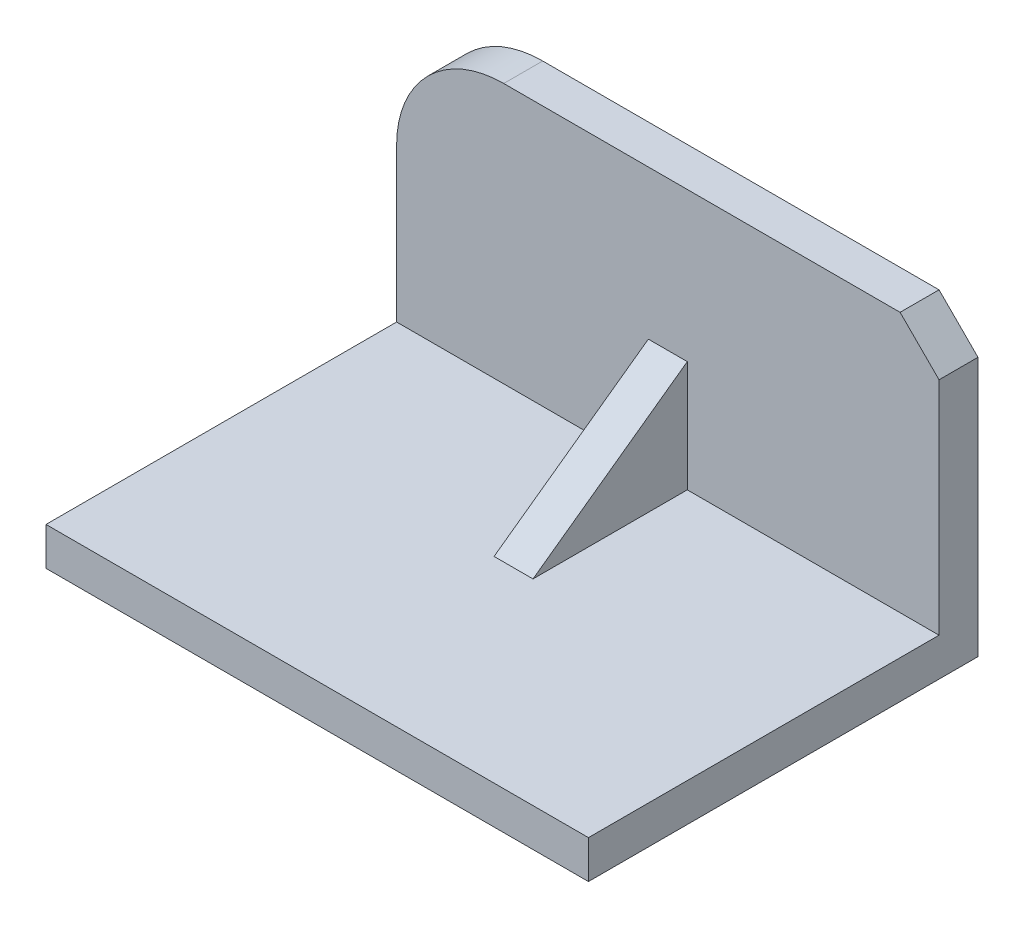
SolidWorks part; units mm, degrees
ref_plane "Front Plane" through (0, 0, 0) normal (0, 0, 1) x (1, 0, 0)
ref_plane "Top Plane" through (0, 0, 0) normal (0, 1, 0) x (1, 0, 0)
ref_plane "Right Plane" through (0, 0, 0) normal (1, 0, 0) x (0, 0, -1)
sketch "Sketch1" plane through (0, 0, 0) normal (0, 0, 1) x (1, 0, 0)
  line L1 (-42.1183, 38.2775) -> (69.6255, 38.2775)
  line L2 (-69.6255, 10.7703) -> (-69.6255, -38.2775)
  line L3 (-69.6255, -38.2775) -> (69.6255, -38.2775)
  line L4 (69.6255, 38.2775) -> (69.6255, -38.2775)
  line L5 (-59.0391, 32.4575) -> (69.6255, -38.2775) construction
  line L6 (-69.6255, -38.2775) -> (69.6255, 38.2775) construction
  arc A0 (-42.1183, 38.2775) -> (-69.6255, 10.7703) centre (-42.1183, 10.7703) ccw
  point P0 (0, 0)
extrude "Boss-Extrude1" add sketch "Sketch1" along normal blind 10
chamfer "Chamfer1" distance 10 angle 45 1 edges at (69.6255, 38.2775, 5)
sketch "Sketch2" plane through (0, 0, 10) normal (0, 0, 1) x (1, 0, 0)
  line L0 (69.6255, -38.2775) -> (69.6255, 28.2775) construction
  line L1 (-69.6255, -38.2775) -> (69.6255, -38.2775)
  line L2 (-69.6255, -38.2775) -> (-69.6255, -28.5062)
  line L3 (-69.6255, -28.5062) -> (69.6255, -28.5062)
  line L4 (69.6255, -38.2775) -> (69.6255, -28.5062)
extrude "Boss-Extrude2" add sketch "Sketch2" along normal blind 90
sketch "Sketch3" plane through (0, 0, 0) normal (1, 0, 0) x (0, 0, -1)
  line L0 (-49.6063, -28.5062) -> (-10, 0)
  line L1 (-100, -28.5062) -> (-10, -28.5062) construction
  line L2 (-10, -28.5062) -> (-10, 28.2775) construction
rib "Rib1" sketch "Sketch3" sketch "Sketch3" thickness 10 extrusion direction parallel to sketch draft on no parameters "D1"=10
